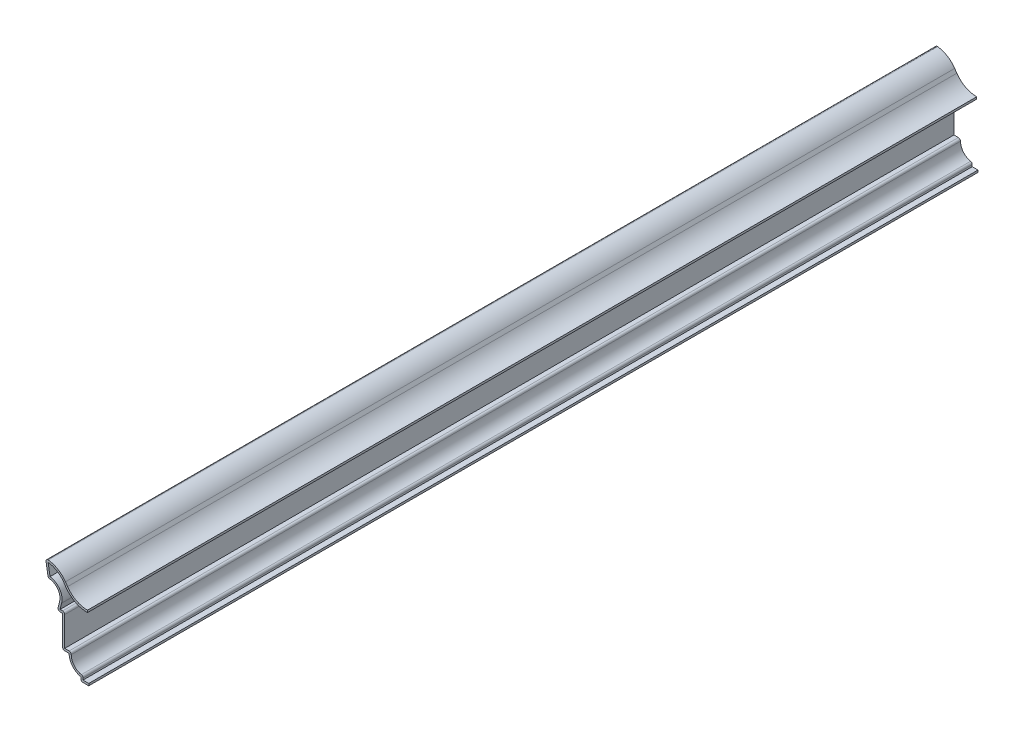
SolidWorks part; units mm, degrees
ref_plane "Front Plane" through (0, 0, 0) normal (0, 0, 1) x (1, 0, 0)
ref_plane "Top Plane" through (0, 0, 0) normal (0, 1, 0) x (1, 0, 0)
ref_plane "Right Plane" through (0, 0, 0) normal (1, 0, 0) x (0, 0, -1)
sketch "Sketch1" plane through (0, 0, 0) normal (0, 0, 1) x (1, 0, 0)
  line L0 (0, 0) -> (-4.7625, 0)
  line L1 (-4.7625, 0) -> (-4.7625, 2.3812)
  line L2 (-11.9062, 11.1125) -> (-15.875, 11.1125)
  line L3 (-15.875, 11.1125) -> (-15.875, 30.1625)
  line L4 (-15.875, 30.1625) -> (-19.05, 30.1625)
  line L5 (-19.05, 30.1625) -> (-17.6823, 35.5478)
  line L6 (-24.6063, 44.45) -> (-26.1937, 53.975)
  line L7 (-14.1402, 47.6173) -> (-12.8473, 45.7277)
  arc A0 (-4.7625, 2.3812) -> (-11.9062, 11.1125) centre (-2.9986, 11.1125) cw
  arc A1 (-17.6823, 35.5478) -> (-24.6063, 44.45) centre (-24.6062, 37.3062) ccw
  arc A2 (-26.1937, 53.975) -> (-14.1402, 47.6173) centre (-26.1938, 39.37) cw
  arc A3 (-12.8473, 45.7277) -> (-0.7938, 39.37) centre (-0.7938, 53.975) ccw
  dimension "D1" = 4.7625
  dimension "D2" = 2.3813
  dimension "D3" = 7.1437
  dimension "D4" = 3.9688
  dimension "D5" = 8.7312
  dimension "D6" = 19.05
  dimension "D7" = 3.175
  dimension "D8" = 14.2875
  dimension "D9" = 9.525
  dimension "D10" = 5.5562
  dimension "D11" = 7.1437
  dimension "D12" = 1.5875
  dimension "D13" = 14.605
  dimension "D14" = 25.4
extrude "Extrude-Thin1" add sketch "Sketch1" against normal blind 539.75 thin
fillet "Fillet1" radius 1.27 8 edges at (-4.7625, 0, -269.875) (-3.4925, 3.4908, -269.875) (-15.875, 11.1125, -269.875) (-10.5299, 12.3825, -269.875) (-14.605, 31.4325, -269.875) (-19.05, 30.1625, -269.875) (-24.6062, 44.45, -269.875) (-26.1937, 53.975, -269.875)
